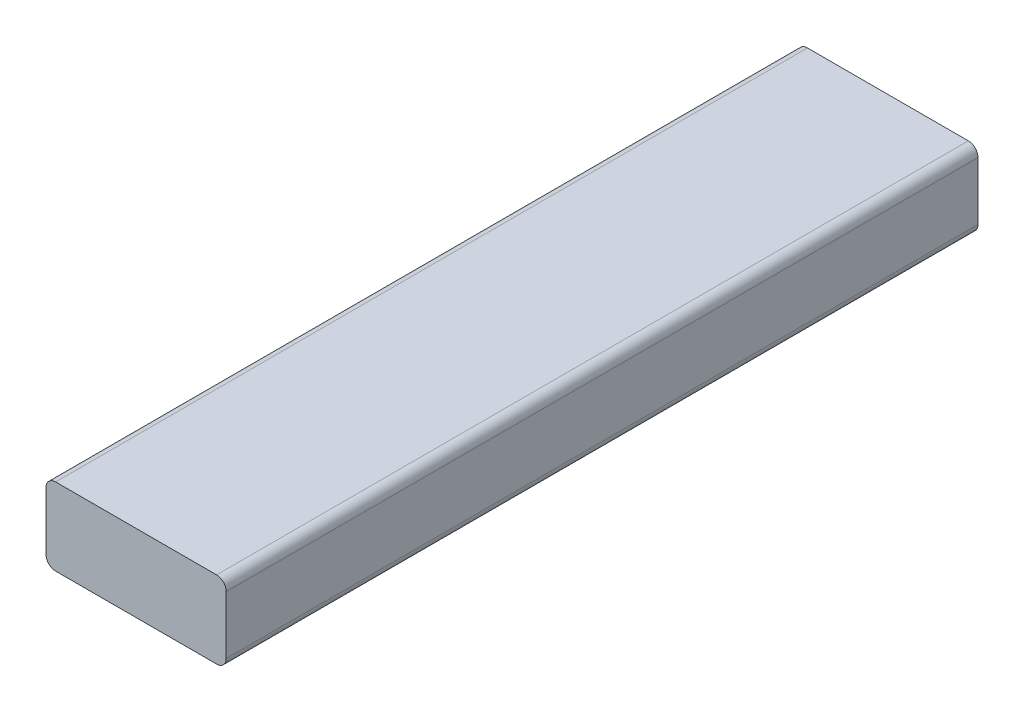
SolidWorks part; units mm, degrees
material "Pine"
ref_plane "Front Plane" through (0, 0, 0) normal (0, 0, 1) x (1, 0, 0)
ref_plane "Top Plane" through (0, 0, 0) normal (0, 1, 0) x (1, 0, 0)
ref_plane "Right Plane" through (0, 0, 0) normal (1, 0, 0) x (0, 0, -1)
sketch "Sketch1" plane through (0, 0, 0) normal (0, 0, 1) x (1, 0, 0)
  line L1 (458.9322, 38.1) -> (547.8322, 38.1)
  line L2 (458.9322, 38.1) -> (458.9322, 0)
  line L3 (458.9322, 0) -> (547.8322, 0)
  line L4 (547.8322, 38.1) -> (547.8322, 0)
  line L5 (547.8322, 38.1) -> (547.8322, 465.6941) construction
  line L6 (781.7306, 0) -> (204.9322, 0) construction
extrude "Boss-Extrude1" add sketch "Sketch1" along normal up to surface (370.7765 mm away)
fillet "Fillet1" radius 4.7625 4 edges at (547.8322, 38.1, 185.3883) (547.8322, 0, 185.3883) (458.9322, 38.1, 185.3883) (458.9322, 0, 185.3883)
